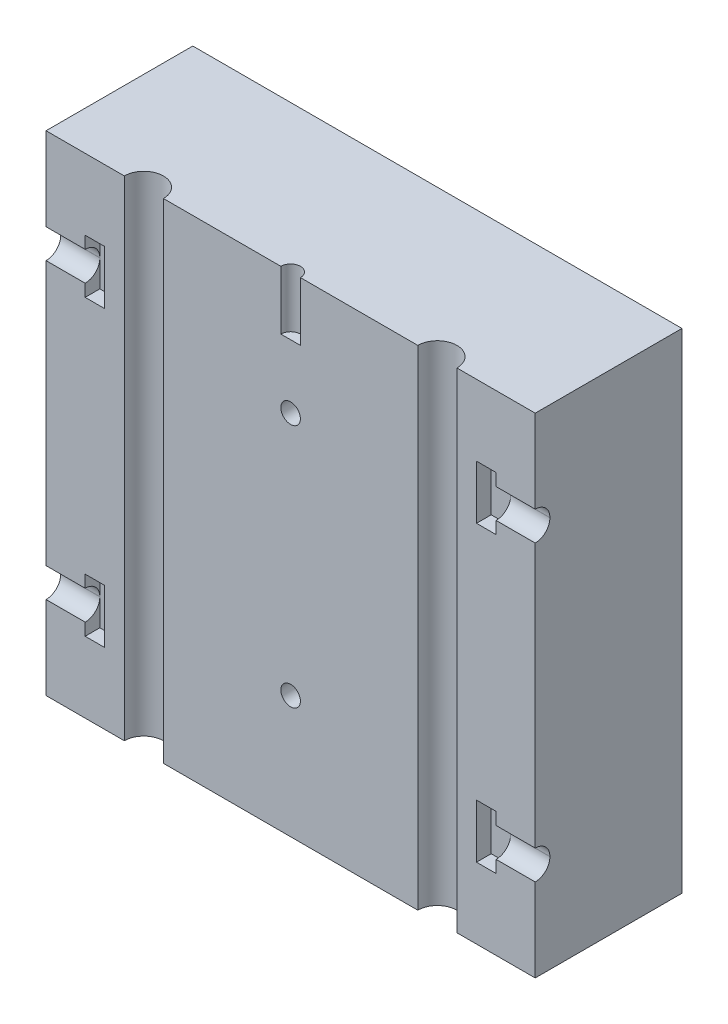
SolidWorks part; units mm, degrees
ref_plane "Plan de face" through (0, 0, 0) normal (0, 0, 1) x (1, 0, 0)
ref_plane "Plan de dessus" through (0, 0, 0) normal (0, 1, 0) x (1, 0, 0)
ref_plane "Plan de droite" through (0, 0, 0) normal (1, 0, 0) x (0, 0, -1)
sketch "Esquisse1" plane through (0, 0, 0) normal (0, 0, 1) x (1, 0, 0)
  line L0 (17.9177, 25) -> (30.2033, 25) construction
  line L1 (0, 0) -> (50, 0)
  line L2 (0, 0) -> (0, 50)
  line L3 (0, 50) -> (50, 50)
  line L4 (50, 0) -> (50, 50)
  line L5 (25, 82.493) -> (25, -3.859) construction
extrude "Extrusion1" add sketch "Esquisse1" along normal blind 15
sketch "Esquisse2" plane through (0, 50, 0) normal (0, 1, 0) x (-1, 0, 0)
  line L0 (-25, -2.8423) -> (-25, 10.3145) construction
  line L1 (-10, 10.3145) -> (-10, -1.749) construction
  line L2 (1.6579, 15) -> (-41.5071, 15) construction
  circle A0 centre (-10, 15) radius 2
  circle A1 centre (-40, 15) radius 2
  dimension "D1" = 15
extrude "Enlèv. mat.-Extru.1" cut sketch "Esquisse2" against normal through all
sketch "Esquisse3" plane through (0, 0, 15) normal (0, 0, 1) x (1, 0, 0)
  line L0 (-6.9611, 50) -> (52.882, 50) construction
  line L1 (-6.9611, 0) -> (52.882, 0) construction
  line L2 (0, 53.8943) -> (0, -3.9793) construction
  line L3 (25, 53.8943) -> (25, -3.0703) construction
  line L4 (-6.9611, 25) -> (55.003, 25) construction
  line L5 (-6.9611, 10) -> (34.3988, 10) construction
  line L6 (6, -3.0703) -> (6, 16.4853) construction
  line L7 (4, -3.0703) -> (4, 16.4853) construction
  line L8 (-6.6638, 11.5) -> (10.0386, 11.5) construction
  line L9 (-6.9611, 8.5) -> (10.0386, 8.5) construction
  line L10 (3.2114, 12.75) -> (6.4884, 12.75) construction
  line L11 (-1.135, 11.5) -> (4, 11.5)
  line L12 (-1.135, 11.5) -> (-1.135, 8.5)
  line L13 (-1.135, 8.5) -> (4, 8.5)
  line L14 (-1.135, 38.5) -> (-1.135, 41.5)
  line L15 (3.2114, 7.25) -> (6.4884, 7.25) construction
  line L16 (4, 8.5) -> (4, 7.25)
  line L17 (4, 12.75) -> (6, 12.75)
  line L18 (4, 12.75) -> (4, 11.5)
  line L19 (4, 7.25) -> (6, 7.25)
  line L20 (6, 12.75) -> (6, 7.25)
  line L21 (-1.135, 41.5) -> (4, 41.5)
  line L22 (-1.135, 38.5) -> (4, 38.5)
  line L23 (4, 37.25) -> (6, 37.25)
  line L24 (4, 37.25) -> (4, 38.5)
  line L25 (6, 37.25) -> (6, 42.75)
  line L26 (4, 42.75) -> (6, 42.75)
  line L27 (4, 41.5) -> (4, 42.75)
  line L28 (46, 42.75) -> (44, 42.75)
  line L29 (46, 41.5) -> (46, 42.75)
  line L30 (51.135, 41.5) -> (46, 41.5)
  line L31 (51.135, 38.5) -> (51.135, 41.5)
  line L32 (51.135, 38.5) -> (46, 38.5)
  line L33 (44, 37.25) -> (44, 42.75)
  line L34 (46, 37.25) -> (44, 37.25)
  line L35 (46, 37.25) -> (46, 38.5)
  line L36 (46, 12.75) -> (44, 12.75)
  line L37 (44, 12.75) -> (44, 7.25)
  line L38 (46, 7.25) -> (44, 7.25)
  line L39 (51.135, 8.5) -> (46, 8.5)
  line L40 (51.135, 11.5) -> (46, 11.5)
  line L41 (46, 12.75) -> (46, 11.5)
  line L42 (46, 8.5) -> (46, 7.25)
  line L43 (51.135, 11.5) -> (51.135, 8.5)
  dimension "D1" = 10
  dimension "D2" = 1.5
  dimension "D3" = 3
  dimension "D4" = 6
  dimension "D5" = 2
  dimension "D6" = 2.75
  dimension "D7" = 2.75
extrude "Enlèv. mat.-Extru.3" cut sketch "Esquisse3" against normal blind 1.5
fillet "Congé1" radius 1.49 1 edges at (2, 11.5, 13.5)
fillet "Congé2" radius 1.49 7 edges at (48, 11.5, 13.5) (48, 8.5, 13.5) (2, 8.5, 13.5) (2, 38.5, 13.5) (2, 41.5, 13.5) (48, 41.5, 13.5) (48, 38.5, 13.5)
sketch "Esquisse4" plane through (0, 50, 0) normal (0, 1, 0) x (-1, 0, 0)
  line L0 (-55.136, 15) -> (3.6621, 15) construction
  line L1 (-25, 22.9753) -> (-25, -4.8724) construction
  line L2 (0, -10.6125) -> (0, 22.9753) construction
  circle A0 centre (-25, 15) radius 1
  dimension "D1" = 25
extrude "Enlèv. mat.-Extru.4" cut sketch "Esquisse4" against normal blind 6
sketch "Esquisse5" plane through (0, 0, 15) normal (0, 0, 1) x (1, 0, 0)
  line L0 (-6.4307, 0) -> (57.7479, 0) construction
  line L1 (0, -5.2598) -> (0, 53.9426) construction
  line L2 (25, 53.9426) -> (25, -5.2598) construction
  line L3 (17.06, 25) -> (33.8181, 25) construction
  line L4 (18.1577, 37.5) -> (31.9155, 37.5) construction
  circle A0 centre (25, 37.5) radius 1
  circle A1 centre (25, 12.5) radius 1
extrude "Enlèv. mat.-Extru.5" cut sketch "Esquisse5" against normal blind 6
